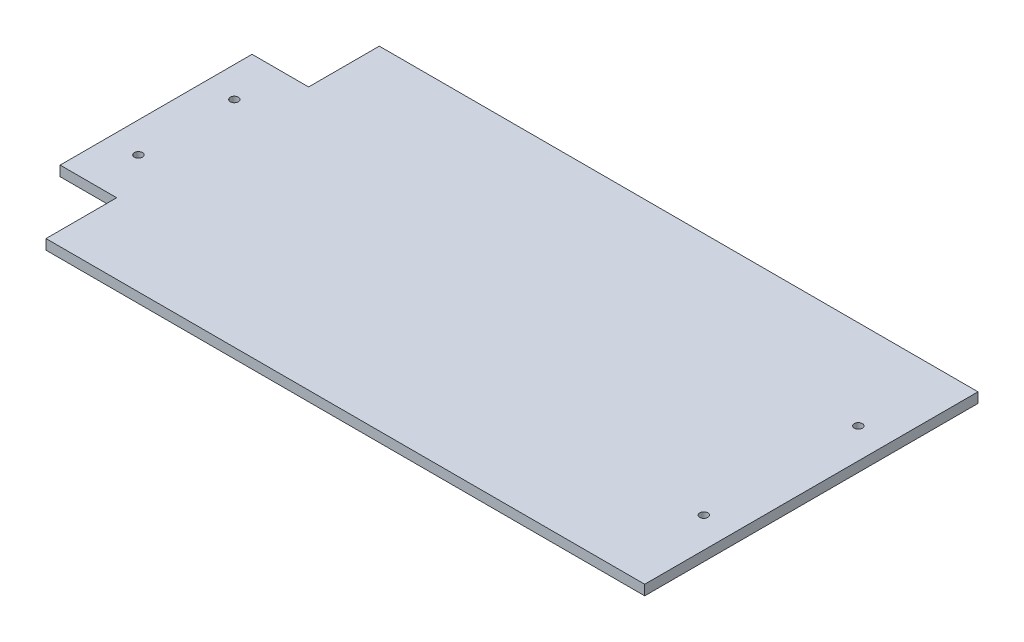
SolidWorks part; units mm, degrees
ref_plane "Front Plane" through (0, 0, 0) normal (0, 0, 1) x (1, 0, 0)
ref_plane "Top Plane" through (0, 0, 0) normal (0, 1, 0) x (1, 0, 0)
ref_plane "Right Plane" through (0, 0, 0) normal (1, 0, 0) x (0, 0, -1)
sketch "Sketch1" plane through (0, 0, 0) normal (0, 1, 0) x (1, 0, 0)
  line L1 (162.2, -82.5) -> (162.2, 82.5)
  line L2 (162.2, 82.5) -> (-134.2, 82.5)
  line L3 (-162.2, 47.5) -> (-162.2, -47.5)
  line L4 (-162.2, 47.5) -> (-134.2, 47.5)
  line L5 (-134.2, 47.5) -> (-134.2, 82.5)
  line L6 (-162.2, 0) -> (162.2, 0) construction
  line L7 (162.2, -82.5) -> (-134.2, -82.5)
  line L8 (-134.2, -47.5) -> (-134.2, -82.5)
  line L9 (-162.2, -47.5) -> (-134.2, -47.5)
  point P4 (0, 0)
  dimension "D1" = 82.5
  dimension "D2" = 324.4
  dimension "D3" = 28
  dimension "D4" = 35
extrude "Boss-Extrude1" add sketch "Sketch1" along normal blind 5
sketch "Sketch2" plane through (0, 5, 0) normal (0, 1, 0) x (1, 0, 0)
  line L0 (-147.2, 65.1841) -> (-147.2, -74.7001) construction
  line L1 (-162.2, 47.5) -> (-162.2, -47.5) construction
  line L2 (-134.2, 47.5) -> (-162.2, 47.5) construction
  line L3 (147.2, 107.6125) -> (147.2, -120.2355) construction
  line L4 (-206.6899, 0) -> (190.6223, 0) construction
  circle A0 centre (-147.2, 23.75) radius 2
  circle A1 centre (147.2, 38.25) radius 2
  circle A2 centre (147.2, -38.25) radius 2
  circle A3 centre (-147.2, -23.75) radius 2
  dimension "D2" = 4
  dimension "D6" = 4
  dimension "D1" = 15
  dimension "D3" = 23.75
  dimension "D4" = 294.4
  dimension "D5" = 14.5
extrude "Cut-Extrude1" cut sketch "Sketch2" against normal blind 5
